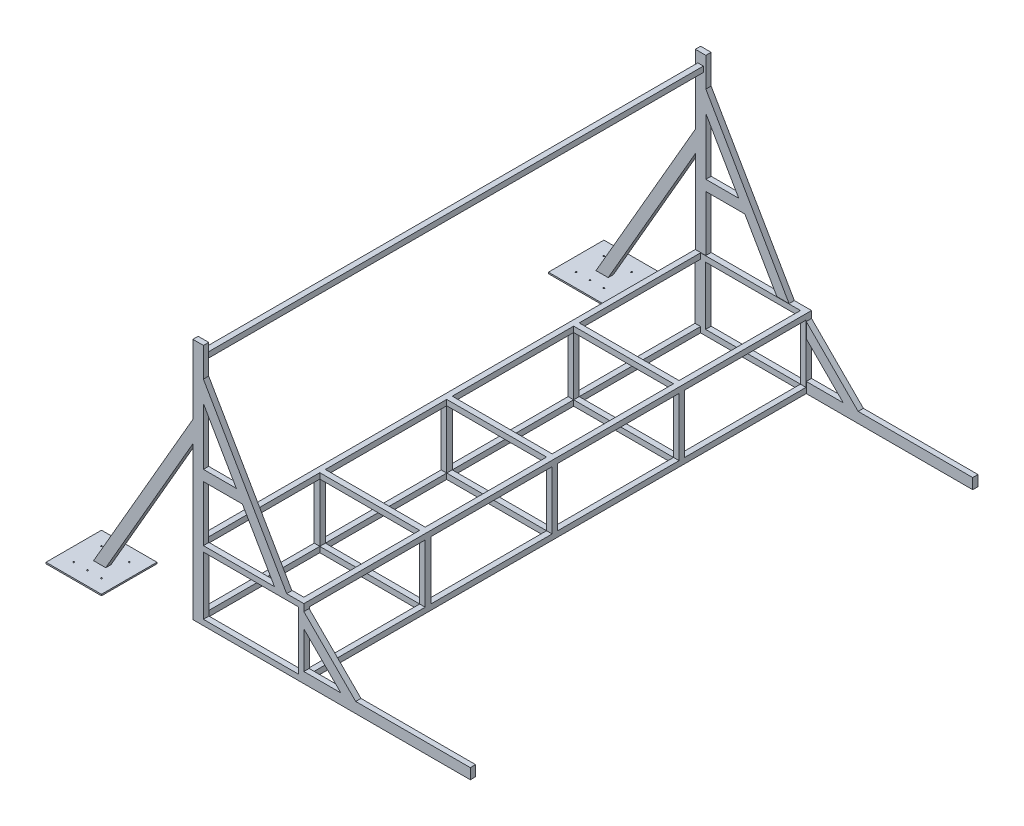
SolidWorks part; units mm, degrees
ref_plane "Front Plane" through (0, 0, 0) normal (0, 0, 1) x (1, 0, 0)
ref_plane "Top Plane" through (0, 0, 0) normal (0, 1, 0) x (1, 0, 0)
ref_plane "Right Plane" through (0, 0, 0) normal (1, 0, 0) x (0, 0, -1)
sketch "Sketch1" plane through (0, 0, 0) normal (0, 0, 1) x (1, 0, 0)
  line L0 (0, 0) -> (800, 0)
  line L1 (55, 0) -> (-55, 0) construction
  line L4 (800, 500) -> (800, 1426.2248) construction
  line L6 (0, 0) -> (0, 500)
  line L7 (0, 500) -> (800, 500)
  line L8 (800, 500) -> (800, 0)
  line L9 (0, 500) -> (0, 2000)
  line L10 (800, 500) -> (2630, 3669.653)
  line L11 (1715, 2084.8265) -> (0, 2000) construction
  line L12 (800, 0) -> (5182.5126, 0) construction
  line L13 (2805.4283, 4100) -> (3005.4283, 4100)
  line L14 (5.4283, 4100) -> (205.4283, 4100)
  line L15 (5.4283, 4100) -> (5.4283, 3700)
  line L16 (5.4283, 3700) -> (205.4283, 3700)
  line L17 (205.4283, 4100) -> (205.4283, 3700)
  line L18 (5.4283, 4100) -> (205.4283, 3700) construction
  line L19 (5.4283, 3700) -> (205.4283, 4100) construction
  line L20 (2805.4283, 4100) -> (2805.4283, 3700)
  line L21 (2805.4283, 3700) -> (3005.4283, 3700)
  line L22 (3005.4283, 4100) -> (3005.4283, 3700)
  line L23 (2805.4283, 4100) -> (3005.4283, 3700) construction
  line L24 (2805.4283, 3700) -> (3005.4283, 4100) construction
  line L25 (800, 500) -> (784.4115, 509)
  line L26 (1715, 2084.8265) -> (1160.2235, 2405.1269) construction
  line L27 (2630, 3669.653) -> (2630, 2940.232) construction
  line L28 (2630, 3669.653) -> (3156.2133, 3365.8436) construction
  line L29 (784.4115, 509) -> (2614.4115, 3678.653)
  line L30 (2614.4115, 3678.653) -> (2630, 3669.653)
  line L31 (5605.4283, 4100) -> (5805.4283, 4100)
  line L32 (5605.4283, 4100) -> (5605.4283, 3700)
  line L33 (5605.4283, 3700) -> (5805.4283, 3700)
  line L34 (5805.4283, 4100) -> (5805.4283, 3700)
  line L35 (5605.4283, 4100) -> (5805.4283, 3700) construction
  line L36 (5605.4283, 3700) -> (5805.4283, 4100) construction
  point P5 (105.4283, 3900)
  point P17 (2905.4283, 3900)
  point P22 (5705.4283, 3900)
  dimension "D1" = 800
  dimension "D2" = 500
  dimension "D3" = 1500
  dimension "D4" = 3660
  dimension "D5" = 30
  dimension "D6" = 3669.653
  dimension "D7" = 2630
  dimension "D8" = 1717.0965
  dimension "D9" = 200
  dimension "D10" = 400
  dimension "D11" = 3700
  dimension "D12" = 200
  dimension "D13" = 400
  dimension "D17" = 90
  dimension "D18" = 32.832
  dimension "D19" = 90
  dimension "D14" = 2600
  dimension "D15" = 18
  dimension "D16" = 200
  dimension "D20" = 400
  dimension "D21" = 2600
extrude "Boss-Extrude5" add sketch "Sketch1" along normal blind 3660 contours L8 L7 L6 L0 | L30 L29 L25 L10
ref_plane "Plane1" through (0, 0, 1830) normal (0, 0, 1) x (1, 0, 0)
sketch "Sketch3" plane through (0, 0, 0) normal (0, 0, 1) x (1, 0, 0)
  line L0 (0, 0) -> (-1677.1081, 0) construction
  line L1 (0, 500) -> (76, 500)
  line L2 (0, 500) -> (0, 1098)
  line L3 (0, 1750) -> (76, 1750)
  line L4 (76, 500) -> (76, 900)
  line L5 (0, 1250) -> (-721.6878, 0)
  line L6 (0, 1098) -> (-633.9306, 0)
  line L7 (0, 1250) -> (0, 1750)
  line L8 (0, 500) -> (0, 2000) construction
  line L9 (-633.9306, 0) -> (-721.6878, 0)
  line L10 (76, 1539.2305) -> (676, 500)
  line L11 (0, 500) -> (800, 500) construction
  line L12 (76, 1387.2305) -> (313.424, 976)
  line L14 (676, 500) -> (588.2428, 500)
  line L15 (76, 1539.2305) -> (76, 1750)
  line L16 (76, 976) -> (313.424, 976)
  line L17 (76, 900) -> (357.3027, 900)
  line L18 (76, 976) -> (76, 1387.2305)
  line L19 (357.3027, 900) -> (588.2428, 500)
  line L20 (800, 450) -> (1174, 76)
  line L21 (800, 500) -> (800, 0) construction
  line L23 (1066.5198, 76) -> (800, 342.5198)
  line L24 (800, 342.5198) -> (800, 450)
  line L25 (1174, 76) -> (2000, 76)
  line L26 (800, 0) -> (2000, 0)
  line L27 (800, 0) -> (800, 76)
  line L28 (800, 76) -> (1066.5198, 76)
  line L29 (2000, 0) -> (2000, 76)
  point P21 (376, 1019.6152)
  point P22 (-677.8092, 0)
  point P36 (1291.3836, 112.17)
  point P37 (0, 0)
  dimension "D3" = 76
  dimension "D4" = 1200
  dimension "D6" = 60
  dimension "D1" = 76
  dimension "D5" = 76
  dimension "D7" = 60
  dimension "D2" = 1750
  dimension "D8" = 76
  dimension "D9" = 400
  dimension "D10" = 76
  dimension "D11" = 1200
  dimension "D12" = 76
  dimension "D13" = 50
  dimension "D14" = 45
extrude "Boss-Extrude2" add sketch "Sketch3" along normal blind 38
mirror "Mirror1" about plane through (0, 0, 1830) normal (0, 0, 1) of "Boss-Extrude2"
sketch "Sketch4" plane through (0, 0, 3660) normal (0, 0, 1) x (1, 0, 0)
  line L0 (800, 500) -> (800, 0) construction
  line L1 (76, 460) -> (760, 460)
  line L2 (76, 460) -> (76, 40)
  line L3 (76, 40) -> (760, 40)
  line L4 (760, 460) -> (760, 40)
  line L5 (0, 0) -> (800, 0) construction
  line L7 (0, 500) -> (800, 500) construction
  line L8 (0, 0) -> (0, 1098) construction
  dimension "D3" = 76
  dimension "D1" = 40
  dimension "D2" = 40
  dimension "D4" = 40
extrude "Cut-Extrude1" cut sketch "Sketch4" against normal through all
sketch "Sketch5" plane through (0, 0, 1830) normal (0, 0, 1) x (1, 0, 0)
  line L0 (40, 500) -> (40, 460)
  line L1 (40, 460) -> (0, 460)
  line L2 (0, 460) -> (0, 40)
  line L3 (0, 40) -> (40, 40)
  line L4 (40, 40) -> (40, 0)
  line L5 (40, 0) -> (760, 0)
  line L6 (760, 0) -> (760, 40)
  line L7 (760, 40) -> (800, 40)
  line L8 (800, 40) -> (800, 460)
  line L9 (800, 460) -> (760, 460)
  line L10 (760, 460) -> (760, 500)
  line L11 (760, 500) -> (40, 500)
  line L12 (800, 500) -> (800, 0) construction
  line L13 (0, 500) -> (800, 500) construction
  line L14 (0, 0) -> (0, 500) construction
  line L15 (0, 0) -> (800, 0) construction
  line L17 (0, 0) -> (0, 1098) construction
  dimension "D1" = 40
extrude "Cut-Extrude2" cut sketch "Sketch5" against normal offset from surface 40 and the other way offset from surface (1790 mm away) 40 up to face at (418, 250, 0)
sketch "Sketch7" plane through (367.9052, -212.4102, 0) normal (-0.866, 0.5, 0) x (0, 0, 1)
  line L0 (1830, 833.0127) -> (0, 833.0127)
  line L2 (0, 833.0127) -> (0, 4493.0127)
  line L3 (0, 4493.0127) -> (1830, 4493.0127)
  line L5 (1830, 4493.0127) -> (1830, 4455.0127)
  line L6 (1830, -275) -> (1830, 275) construction
  line L7 (1830, 4455.0127) -> (38, 4455.0127)
  line L8 (38, 4455.0127) -> (38, 871.0127)
  line L9 (38, 871.0127) -> (1830, 871.0127)
  line L10 (1830, 871.0127) -> (1830, 833.0127)
  dimension "D1" = 38
  dimension "D2" = 38
  dimension "D3" = 38
extrude "Boss-Extrude3" add sketch "Sketch7" along normal blind 76
mirror "Mirror2" about plane through (0, 0, 1830) normal (0, 0, 1) of "Boss-Extrude3"
sketch "Sketch8" plane through (367.9052, -212.4102, 0) normal (-0.866, 0.5, 0) x (0, 0, 1)
  line L1 (0, 833.0127) -> (2440, 833.0127)
  line L2 (0, 833.0127) -> (0, 2053.0127)
  line L3 (0, 2053.0127) -> (2440, 2053.0127)
  line L4 (2440, 833.0127) -> (2440, 2053.0127)
  line L5 (2440, 833.0127) -> (3660, 833.0127)
  line L6 (2440, 833.0127) -> (2440, 3273.0127)
  line L7 (2440, 3273.0127) -> (3660, 3273.0127)
  line L8 (3660, 833.0127) -> (3660, 3273.0127)
  line L9 (0, 833.0127) -> (0, 4493.0127) construction
  line L10 (2440, 3273.0127) -> (3660, 3273.0127)
  line L11 (2440, 3273.0127) -> (2440, 4493.0127)
  line L12 (2440, 4493.0127) -> (3660, 4493.0127)
  line L13 (3660, 3273.0127) -> (3660, 4493.0127)
  line L14 (2440, 3273.0127) -> (0, 3273.0127)
  line L15 (2440, 3273.0127) -> (2440, 2053.0127)
  line L16 (2440, 2053.0127) -> (0, 2053.0127)
  line L17 (0, 3273.0127) -> (0, 2053.0127)
  line L18 (2440, 3273.0127) -> (0, 3273.0127)
  line L19 (2440, 3273.0127) -> (2440, 4493.0127)
  line L20 (2440, 4493.0127) -> (0, 4493.0127)
  line L21 (0, 3273.0127) -> (0, 4493.0127)
  dimension "D1" = 1220
  dimension "D2" = 2440
  dimension "D3" = 2440
  dimension "D4" = 1220
  dimension "D5" = 1220
sketch "Sketch9" plane through (0, 0, 0) normal (0, -1, 0) x (1, 0, 0)
  line L0 (-721.6878, 3660) -> (-633.9306, 3660) construction
  line L1 (-477.8092, 3841) -> (-877.8092, 3841)
  line L2 (-477.8092, 3841) -> (-477.8092, 3441)
  line L3 (-477.8092, 3441) -> (-877.8092, 3441)
  line L4 (-877.8092, 3841) -> (-877.8092, 3441)
  line L5 (-477.8092, 3841) -> (-877.8092, 3441) construction
  line L6 (-477.8092, 3441) -> (-877.8092, 3841) construction
  line L7 (-677.8092, 3622) -> (-677.8092, 3660) construction
  line L8 (-721.6878, 3622) -> (-633.9306, 3622) construction
  line L9 (275, 1830) -> (-275, 1830) construction
  line L10 (-477.8092, -181) -> (-477.8092, 219)
  line L11 (-477.8092, 219) -> (-877.8092, 219)
  line L12 (-877.8092, -181) -> (-877.8092, 219)
  line L13 (-477.8092, -181) -> (-877.8092, -181)
  point P0 (-677.8092, 3641)
  point P11 (-677.8092, 3641)
  dimension "D1" = 400
  dimension "D2" = 400
extrude "Boss-Extrude6" add sketch "Sketch9" against normal blind 10
sketch "Sketch10" plane through (0, 0, 0) normal (0, 0, 1) x (1, 0, 0)
  line L1 (4364.3674, 1800) -> (4789.2316, 1800)
  line L2 (4364.3674, 1800) -> (4364.3674, 0)
  line L3 (4364.3674, 0) -> (4789.2316, 0)
  line L4 (4789.2316, 1800) -> (4789.2316, 0)
  line L5 (4364.3674, 1800) -> (4789.2316, 0) construction
  line L6 (4364.3674, 0) -> (4789.2316, 1800) construction
  point P0 (4576.7995, 900)
  dimension "D1" = 1800
sketch "Sketch11" plane through (0, 0, 38) normal (0, 0, 1) x (1, 0, 0)
  line L0 (76, 1750) -> (0, 1750) construction
  line L1 (58, 1634) -> (18, 1634)
  line L2 (58, 1634) -> (58, 1674)
  line L3 (58, 1674) -> (18, 1674)
  line L4 (18, 1634) -> (18, 1674)
  line L5 (58, 1634) -> (18, 1674) construction
  line L6 (58, 1674) -> (18, 1634) construction
  line L7 (0, 1750) -> (0, 1250) construction
  point P0 (38, 1654)
  dimension "D1" = 40
  dimension "D2" = 76
  dimension "D3" = 18
extrude "Boss-Extrude7" add sketch "Sketch11" along normal up to surface (3584 mm away) up to face at (155.1413, 1113.0768, 3622)
sketch "Sketch12" plane through (0, 40, 0) normal (0, 1, 0) x (1, 0, 0)
  line L1 (0, 0) -> (40, 0)
  line L2 (0, 0) -> (0, -40)
  line L3 (0, -40) -> (40, -40)
  line L4 (40, 0) -> (40, -40)
  line L5 (0, 0) -> (40, -40) construction
  line L6 (0, -40) -> (40, 0) construction
  line L7 (40, -40) -> (40, -3620) construction
  line L8 (0, -40) -> (0, -3620) construction
  line L9 (0, 0) -> (2000, 0) construction
  point P0 (20, -20)
extrude "Boss-Extrude8" add sketch "Sketch12" along normal up to surface (420 mm away) up to face at (20, 460, 1830)
pattern_linear "LPattern1" count 4 spacing 915 along (0, 0, 1) count 2 spacing 760 along (1, 0, 0) of "Boss-Extrude8"
sketch "Sketch13" plane through (760, 0, 0) normal (-1, 0, 0) x (0, 0, 1)
  line L0 (0, 1250) -> (0, 0) construction
  line L1 (0, 500) -> (40, 500)
  line L2 (0, 500) -> (0, 460)
  line L3 (0, 460) -> (40, 460)
  line L4 (40, 500) -> (40, 460)
  line L5 (0, 500) -> (40, 460) construction
  line L6 (0, 460) -> (40, 500) construction
  line L7 (3660, 500) -> (0, 500) construction
  point P0 (20, 480)
  dimension "D1" = 40
extrude "Boss-Extrude9" add sketch "Sketch13" along normal up to surface (760 mm away) up to face at (0, 250, 3202.5)
pattern_linear "LPattern2" count 4 spacing 915 along (0, 0, 1) count 2 spacing 460 along (0, -1, 0) of "Boss-Extrude9"
sketch "Sketch14" plane through (0, 0, 3660) normal (0, 0, 1) x (1, 0, 0)
  line L0 (676, 500) -> (800, 500) construction
  line L1 (617.1788, 500) -> (4758.0267, 500)
  line L2 (617.1788, 500) -> (617.1788, 4035.8495)
  line L3 (617.1788, 4035.8495) -> (4758.0267, 4035.8495)
  line L4 (4758.0267, 500) -> (4758.0267, 4035.8495)
extrude "Cut-Extrude3" cut sketch "Sketch14" against normal through all both and the other way through all
hole_wizard "Ø10.0mm Dowel Hole1" positions "3DSketch1" profile "Sketch17" hole size "Ø10.0" standard "ISO" end condition through all
sketch3d "3DSketch1"
  line L0 (-777.8092, 10, 3541) -> (-777.8092, 10, 3441) construction
  line L1 (-877.8092, 10, 3441) -> (-477.8092, 10, 3441) construction
  line L3 (-777.8092, 10, 3541) -> (-877.8092, 10, 3541) construction
  line L4 (-877.8092, 10, 3841) -> (-877.8092, 10, 3441) construction
  point P0 (-777.8092, 10, 3541)
  dimension "D1" = 100
sketch "Sketch17" plane through (-777.8092, 10, 3541) normal (1, 0, 0) x (0, 0, 1)
  line L0 (0, 0) -> (0, 10)
  line L1 (0, 10) -> (5, 10)
  line L2 (5, 10) -> (5, 0)
  line L5 (5, 0) -> (0, 0)
  line L11 (0, -6.35) -> (0, 107.95) construction
  dimension "Thru Hole Dia." = 10
  dimension "Thru Hole Depth" = 10
pattern_linear "LPattern3" count 2 spacing 200 along (0, 0, 1) count 3 spacing 100 along (1, 0, 0) of "Ø10.0mm Dowel Hole1"
mirror "Mirror3" about plane through (0, 0, 1830) normal (0, 0, 1) of "LPattern3", "Ø10.0mm Dowel Hole1"
equation "\"alpha\"= 30deg'\"Wall Angle\""
equation "\"D5@Sketch1\"=\"alpha\""
equation "\"Frame steel height\"= 76mm"
equation "\"Frame steel length\"= 38mm"
equation "\"Support square tube size\"= 40mm"
equation "\"D3@Sketch3\"=\"Frame steel height\""
equation "\"D1@Sketch4\"=\"Support square tube size\""
equation "\"D2@Sketch4\"=\"Support square tube size\""
equation "\"D4@Sketch4\"=\"Support square tube size\""
equation "\"Wall width\"= 3660mm"
equation "\"D1@Cut-Extrude2\"=\"Support square tube size\""
equation "\"D2@Cut-Extrude2\"=\"Support square tube size\""
equation "\"D1@Sketch7\"=\"Frame steel length\""
equation "\"D2@Sketch7\"=\"Frame steel length\""
equation "\"D3@Sketch7\"=\"Frame steel length\""
equation "\"D1@Boss-Extrude3\"=\"Frame steel height\""
equation "\"D1@Boss-Extrude5\"=\"Wall width\""
equation "\"D1@Boss-Extrude6\"=10mm"
equation "\"D1@Sketch3\"=\"Frame steel height\""
equation "\"D1@Sketch5\"=\"Support square tube size\""
equation "\"D3@Sketch4\"=\"Frame steel height\""
equation "\"D1@Sketch11\"=\"Support square tube size\""
equation "\"D2@Sketch11\"=\"Frame steel height\""
equation "\"D3@Sketch11\"=(\"Frame steel height\"-\"Support square tube size\")/2"
equation "\"D1@Boss-Extrude2\"=\"Frame steel length\""
equation "\"D5@Sketch3\"=\"Frame steel height\""
equation "\"D3@LPattern1\"=\"Wall width\"/4"
equation "\"D4@LPattern1\"=760"
equation "\"D1@Sketch13\"=\"Support square tube size\""
equation "\"D3@LPattern2\"=\"Wall width\"/4"
equation "\"D4@LPattern2\"=500-\"Support square tube size\""
equation "\"D8@Sketch3\"=\"Frame steel height\""
equation "\"D10@Sketch3\"=\"Frame steel height\""
equation "\"D12@Sketch3\"=\"Frame steel height\""
